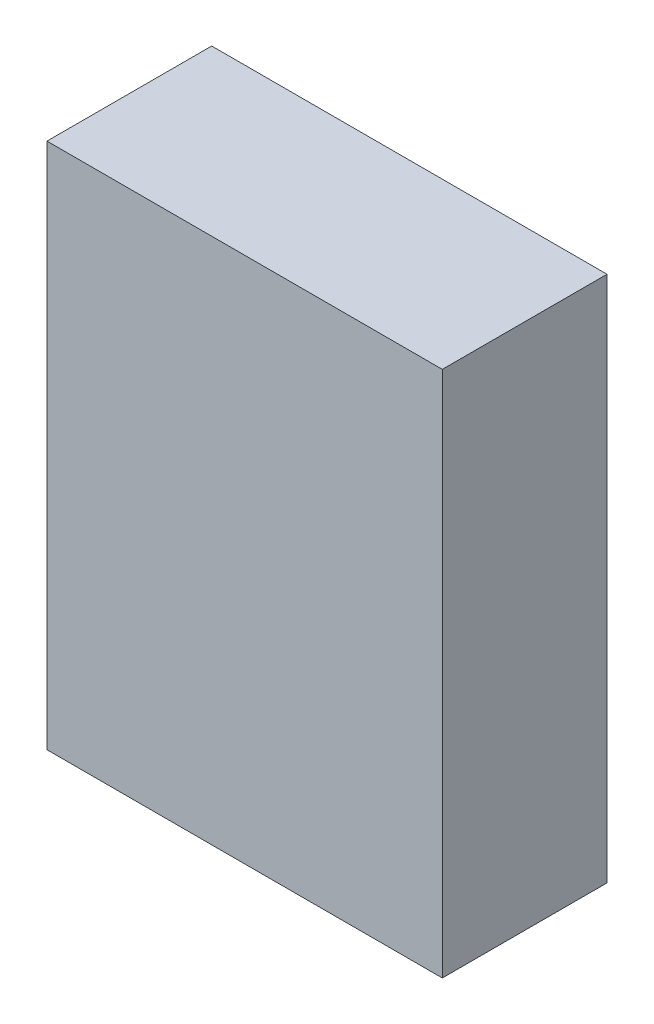
SolidWorks part; units mm, degrees
ref_plane "Alzado" through (0, 0, 0) normal (0, 0, 1) x (1, 0, 0)
ref_plane "Planta" through (0, 0, 0) normal (0, 1, 0) x (1, 0, 0)
ref_plane "Vista lateral" through (0, 0, 0) normal (1, 0, 0) x (0, 0, -1)
sketch "Croquis1" plane through (0, 0, 0) normal (0, 0, 1) x (1, 0, 0)
  line L1 (-300, -400) -> (300, -400)
  line L2 (-300, -400) -> (-300, 400)
  line L3 (-300, 400) -> (300, 400)
  line L4 (300, -400) -> (300, 400)
  line L5 (-300, -400) -> (300, 400) construction
  line L6 (-300, 400) -> (300, -400) construction
  point P0 (0, 0)
  dimension "D1" = 800
  dimension "D2" = 600
extrude "Saliente-Extruir1" add sketch "Croquis1" along normal blind 250
